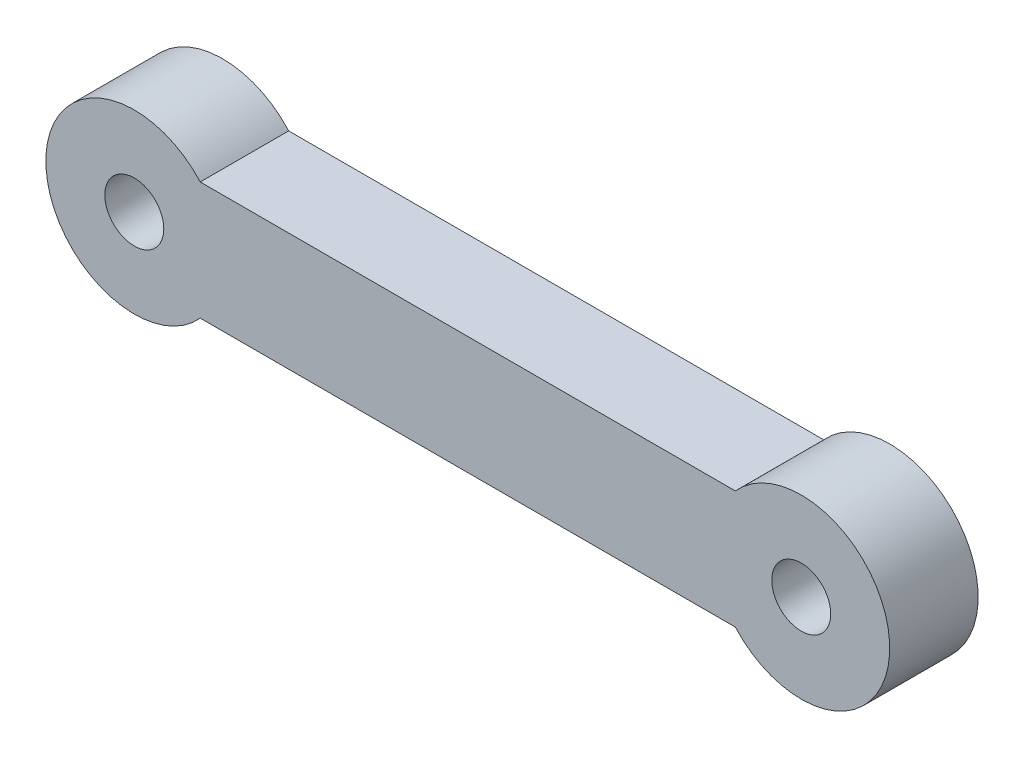
SolidWorks part; units mm, degrees
material "Acrylic (Medium-high impact)"
ref_plane "Front Plane" through (0, 0, 0) normal (0, 0, 1) x (1, 0, 0)
ref_plane "Top Plane" through (0, 0, 0) normal (0, 1, 0) x (1, 0, 0)
ref_plane "Right Plane" through (0, 0, 0) normal (1, 0, 0) x (0, 0, -1)
sketch "Sketch1" plane through (0, 0, 0) normal (0, 0, 1) x (1, 0, 0)
  line L2 (-9.9099, -1.8975) -> (12.7101, -1.8975) construction
  line L3 (-7.6738, 0.1025) -> (-7.6738, -3.8975) construction
  line L4 (10.474, 0.1025) -> (10.474, -3.8975) construction
  line L5 (-7.6738, 0.1025) -> (10.474, 0.1025)
  line L6 (-7.6738, -3.8975) -> (10.474, -3.8975)
  circle A2 centre (-9.9099, -1.8975) radius 1
  circle A3 centre (12.7101, -1.8975) radius 1
  arc A4 (-7.6738, 0.1025) -> (-7.6738, -3.8975) centre (-9.9099, -1.8975) ccw
  arc A5 (10.474, 0.1025) -> (10.474, -3.8975) centre (12.7101, -1.8975) cw
  point P7 (-7.6738, -1.8975)
  dimension "D3" = 2
  dimension "D2" = 22.62
  dimension "D4" = 2
  dimension "D5" = 2
  dimension "D6" = 4
extrude "Boss-Extrude1" add sketch "Sketch1" along normal blind 3
